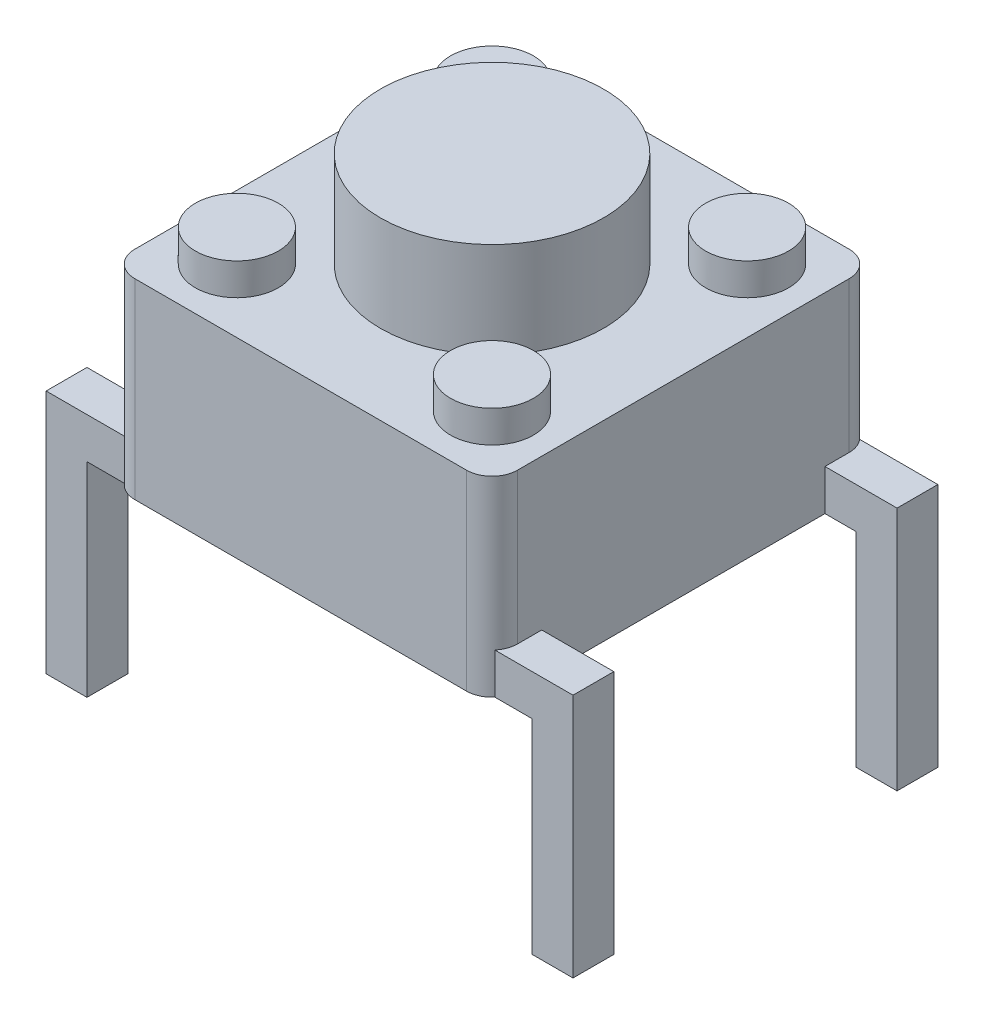
SolidWorks part; units mm, degrees
ref_plane "Front Plane" through (0, 0, 0) normal (0, 0, 1) x (1, 0, 0)
ref_plane "Top Plane" through (0, 0, 0) normal (0, 1, 0) x (1, 0, 0)
ref_plane "Right Plane" through (0, 0, 0) normal (1, 0, 0) x (0, 0, -1)
sketch "Sketch1" plane through (0, 0, 0) normal (0, 1, 0) x (1, 0, 0)
  line L1 (-3, -3) -> (3, -3)
  line L2 (-3, -3) -> (-3, 3)
  line L3 (-3, 3) -> (3, 3)
  line L4 (3, -3) -> (3, 3)
  line L5 (-3, -3) -> (3, 3) construction
  line L6 (-3, 3) -> (3, -3) construction
  point P0 (0, 0)
  dimension "D1" = 6
extrude "Boss-Extrude1" add sketch "Sketch1" along normal blind 3
sketch "Sketch2" plane through (0, 3, 0) normal (0, 1, 0) x (1, 0, 0)
  circle A0 centre (0, 0) radius 1.75
  dimension "D1" = 3.5
extrude "Boss-Extrude2" add sketch "Sketch2" along normal blind 1.5
sketch "Sketch3" plane through (0, 3, 0) normal (0, 1, 0) x (1, 0, 0)
  line L1 (-2, -2) -> (2, -2) construction
  line L2 (-2, -2) -> (-2, 2) construction
  line L3 (-2, 2) -> (2, 2) construction
  line L4 (2, -2) -> (2, 2) construction
  line L5 (-2, -2) -> (2, 2) construction
  line L6 (-2, 2) -> (2, -2) construction
  circle A0 centre (-2, 2) radius 0.65
  circle A1 centre (-2, -2) radius 0.65
  circle A2 centre (2, -2) radius 0.65
  circle A3 centre (2, 2) radius 0.65
  point P0 (0, 0)
  dimension "D1" = 1.3
  dimension "D2" = 4
extrude "Boss-Extrude3" add sketch "Sketch3" along normal blind 0.5
sketch "Sketch4" plane through (0, 0, 0) normal (0, -1, 0) x (1, 0, 0)
  line L1 (-3.81, -2.54) -> (3.81, -2.54) construction
  line L2 (-3.81, -2.54) -> (-3.81, 2.54) construction
  line L3 (-3.81, 2.54) -> (3.81, 2.54) construction
  line L4 (3.81, -2.54) -> (3.81, 2.54) construction
  line L5 (-3.81, -2.54) -> (3.81, 2.54) construction
  line L6 (-3.81, 2.54) -> (3.81, -2.54) construction
  line L7 (-3.49, 2.22) -> (-4.13, 2.22)
  line L8 (-3.49, 2.22) -> (-3.49, 2.86)
  line L9 (-3.49, 2.86) -> (-4.13, 2.86)
  line L10 (-4.13, 2.22) -> (-4.13, 2.86)
  line L11 (-3.49, 2.22) -> (-4.13, 2.86) construction
  line L12 (-3.49, 2.86) -> (-4.13, 2.22) construction
  line L13 (3.49, 2.22) -> (4.13, 2.22)
  line L14 (3.49, 2.22) -> (3.49, 2.86)
  line L15 (3.49, 2.86) -> (4.13, 2.86)
  line L16 (4.13, 2.22) -> (4.13, 2.86)
  line L17 (3.49, 2.22) -> (4.13, 2.86) construction
  line L18 (3.49, 2.86) -> (4.13, 2.22) construction
  line L19 (3.49, -2.86) -> (4.13, -2.86)
  line L20 (3.49, -2.86) -> (3.49, -2.22)
  line L21 (3.49, -2.22) -> (4.13, -2.22)
  line L22 (4.13, -2.86) -> (4.13, -2.22)
  line L23 (3.49, -2.86) -> (4.13, -2.22) construction
  line L24 (3.49, -2.22) -> (4.13, -2.86) construction
  line L25 (-3.49, -2.86) -> (-4.13, -2.86)
  line L26 (-3.49, -2.86) -> (-3.49, -2.22)
  line L27 (-3.49, -2.22) -> (-4.13, -2.22)
  line L28 (-4.13, -2.86) -> (-4.13, -2.22)
  line L29 (-3.49, -2.86) -> (-4.13, -2.22) construction
  line L30 (-3.49, -2.22) -> (-4.13, -2.86) construction
  point P0 (0, 0)
  dimension "D1" = 0.64
  dimension "D2" = 7.62
  dimension "D3" = 5.08
extrude "Boss-Extrude4" add sketch "Sketch4" along normal blind 3.2
fillet "Fillet1" radius 0.4 4 edges at (3, 1.5, -3) (3, 1.5, 3) (-3, 1.5, -3) (-3, 1.5, 3)
sketch "Sketch6" plane through (-4.13, 0, 0) normal (-1, 0, 0) x (0, 0, 1)
  line L1 (-2.86, 0) -> (-2.22, 0)
  line L2 (-2.86, 0) -> (-2.86, 0.64)
  line L3 (-2.86, 0.64) -> (-2.22, 0.64)
  line L4 (-2.22, 0) -> (-2.22, 0.64)
  line L5 (2.22, 0) -> (2.86, 0)
  line L6 (2.22, 0) -> (2.22, 0.64)
  line L7 (2.22, 0.64) -> (2.86, 0.64)
  line L8 (2.86, 0) -> (2.86, 0.64)
  dimension "D1" = 0.64
extrude "Boss-Extrude6" add sketch "Sketch6" against normal up to surface (8.26 mm away) up to face at (4.13, -1.6, 2.54)
